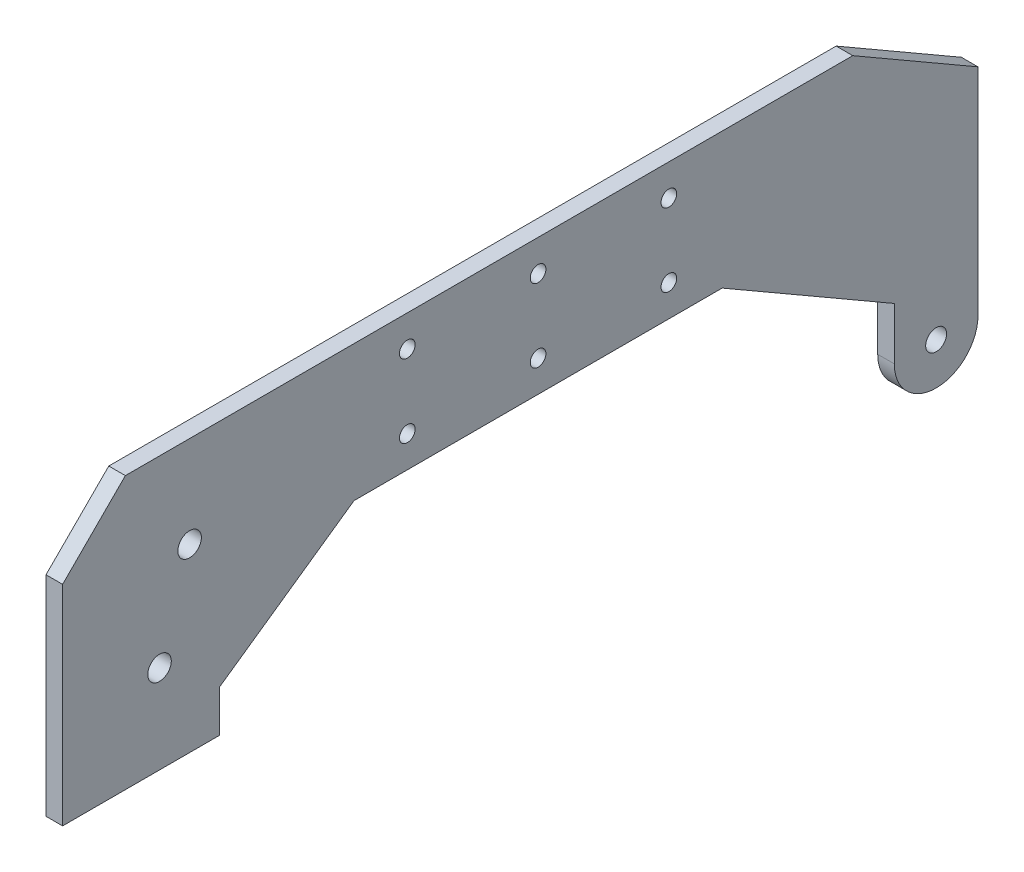
SolidWorks part; units mm, degrees
ref_plane "Front Plane" through (0, 0, 0) normal (0, 0, 1) x (1, 0, 0)
ref_plane "Top Plane" through (0, 0, 0) normal (0, 1, 0) x (1, 0, 0)
ref_plane "Right Plane" through (0, 0, 0) normal (1, 0, 0) x (0, 0, -1)
sketch "Sketch1" plane through (0, 0, 0) normal (1, 0, 0) x (0, 0, -1)
  line L3 (-384.1286, 211.6208) -> (-360.1864, 197.7977)
  line L4 (-360.1864, 197.7977) -> (-360.1864, 156.6208)
  line L5 (-360.1864, 156.6208) -> (-376.1864, 156.6208) construction
  line L6 (-376.1864, 156.6208) -> (-376.1864, 166.6208)
  line L10 (-532.1864, 159.6208) -> (-532.1864, 202.6208) construction
  line L12 (-505.1864, 167.6208) -> (-505.1864, 159.6208)
  line L14 (-535.1864, 199.6208) -> (-535.1864, 159.6208)
  line L16 (-505.1864, 167.6208) -> (-479.4797, 185.6208)
  line L17 (-368.1864, 156.6208) -> (-368.1864, 120.1208) construction
  line L18 (-510.9081, 194.1191) -> (-516.6567, 176.535) construction
  line L20 (-505.1864, 211.6208) -> (-522.1864, 159.6208) construction
  line L21 (-384.1286, 211.6208) -> (-523.1864, 211.6208)
  line L22 (-523.1864, 211.6208) -> (-535.1864, 199.6208)
  line L23 (-505.1864, 159.6208) -> (-535.1864, 159.6208)
  line L25 (-505.1864, 167.6208) -> (-505.1864, 211.6208) construction
  line L27 (-479.4797, 185.6208) -> (-409.0953, 185.6208)
  line L28 (-409.0953, 185.6208) -> (-376.1864, 166.6208)
  line L30 (-419.2875, 205.6208) -> (-469.2875, 205.6208) construction
  line L32 (-444.2875, 211.6208) -> (-444.2875, 185.6208) construction
  line L33 (-419.2875, 191.6208) -> (-469.2875, 191.6208) construction
  line L34 (-419.2875, 198.6208) -> (-469.2875, 198.6208) construction
  line L36 (-469.2875, 211.6208) -> (-469.2875, 185.6208) construction
  line L37 (-419.2875, 211.6208) -> (-419.2875, 185.6208) construction
  arc A0 (-376.1864, 156.6208) -> (-360.1864, 156.6208) centre (-368.1864, 156.6208) ccw
  circle A1 centre (-368.1864, 156.6208) radius 2
  circle A3 centre (-368.1864, 156.6208) radius 8 construction
  circle A5 centre (-419.2875, 205.6208) radius 1.5
  circle A6 centre (-510.9081, 194.1191) radius 2.25
  circle A7 centre (-516.6567, 176.535) radius 2.25
  circle A8 centre (-419.2875, 191.6208) radius 1.5
  circle A9 centre (-469.2875, 205.6208) radius 1.5
  circle A10 centre (-469.2875, 191.6208) radius 1.5
  circle A12 centre (-444.2875, 205.6208) radius 1.5
  circle A13 centre (-444.2875, 191.6208) radius 1.5
  point P12 (-515.0424, 191.1208)
  point P14 (-510.4762, 176.9402)
  point P15 (-518.865, 171.4878)
  point P16 (-513.1331, 187.3132)
  point P34 (-444.2875, 185.6208)
  point P38 (-510.9081, 194.1191)
  point P52 (-444.2875, 205.6208)
  dimension "D2" = 4
  dimension "D1" = 4.5
  dimension "D3" = 4.5
  dimension "D19" = 3
  dimension "D20" = 3
  dimension "D21" = 3
  dimension "D22" = 3
  dimension "D23" = 13
  dimension "D4" = 3
  dimension "D5" = 18.5
  dimension "D6" = 10
  dimension "D7" = 25
  dimension "D8" = 40
  dimension "D9" = 240
  dimension "D10" = 52
  dimension "D11" = 235
  dimension "D13" = 26
  dimension "D14" = 30
  dimension "D15" = 8
  dimension "D16" = 35
  dimension "D17" = 6
  dimension "D18" = 6
  dimension "D27" = 45
  dimension "D28" = 145
  dimension "D29" = 3
extrude "Boss-Extrude1" add sketch "Sketch1" along normal blind 3.175
